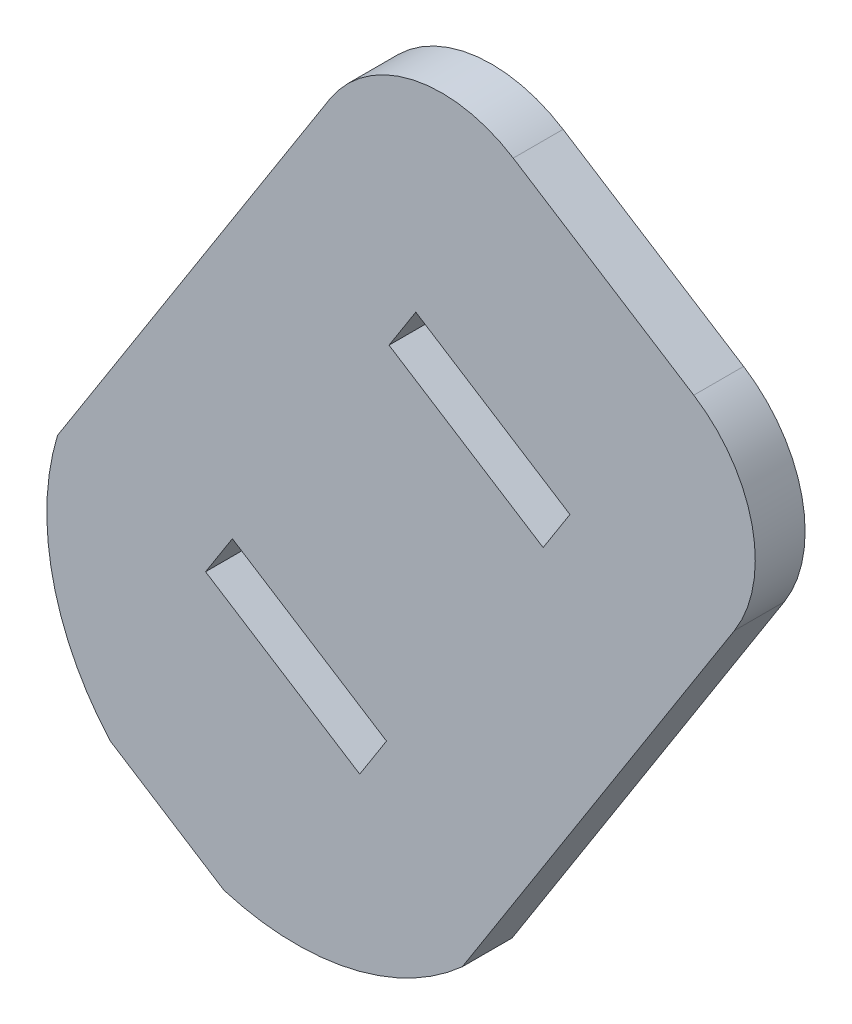
SolidWorks part; units mm, degrees
ref_plane "Alzado" through (0, 0, 0) normal (0, 0, 1) x (1, 0, 0)
ref_plane "Planta" through (0, 0, 0) normal (0, 1, 0) x (1, 0, 0)
ref_plane "Vista lateral" through (0, 0, 0) normal (1, 0, 0) x (0, 0, -1)
sketch "Croquis1" plane through (0, 0, 0) normal (0, 0, 1) x (1, 0, 0)
  circle A0 centre (-35.8759, 30.3873) radius 8
extrude "Saliente-Extruir1" add sketch "Croquis1" against normal up to surface (8 mm away)
sketch "Croquis2" plane through (0, 0, 0) normal (0, 0, 1) x (1, 0, 0)
  line L0 (-45.8794, 41.5645) -> (-50.2335, 34.73)
  line L1 (-13.9527, 57.2587) -> (-20.7873, 61.6128)
  line L2 (-25.8723, 19.2102) -> (-21.5182, 26.0447)
  line L4 (-35.8759, 30.3873) -> (-17.37, 59.4358) construction
  line L5 (-45.8794, 41.5645) -> (-33.849, 60.4485)
  line L6 (-47.0531, 20.3838) -> (-40.2185, 16.0297)
  line L7 (-25.8723, 19.2102) -> (-21.5182, 26.0447)
  line L8 (-54.8587, -26.2892) -> (-43.112, -7.8507)
  line L9 (-20.7873, 61.6128) -> (-22.8035, 62.8973)
  line L10 (-13.9527, 57.2587) -> (-11.9365, 55.9743)
  line L11 (-24.6987, 40.3909) -> (-31.5333, 44.745)
  line L12 (-21.5182, 26.0447) -> (-9.4878, 44.9287)
  arc A0 (-50.2335, 34.73) -> (-47.0531, 20.3838) centre (-35.8759, 30.3873) ccw
  arc A1 (-22.8035, 62.8973) -> (-33.849, 60.4485) centre (-27.1019, 56.1501) ccw
  arc A2 (-11.9365, 55.9743) -> (-9.4878, 44.9287) centre (-16.2349, 49.2271) cw
  arc A3 (-40.2185, 16.0297) -> (-25.8723, 19.2102) centre (-35.8759, 30.3873) ccw
  point P19 (-35.8759, 30.3873)
  dimension "D1" = 4
  dimension "D2" = 8
extrude "Saliente-Extruir2" add sketch "Croquis2" along normal blind 3
sketch "Croquis5" plane through (0, 0, 0) normal (0, 0, 1) x (1, 0, 0)
  line L0 (-19.3905, 46.0278) -> (-21.0024, 43.4976)
  line L5 (-24.0292, 48.9829) -> (-25.6411, 46.4528) construction
  line L7 (-28.6678, 51.9381) -> (-24.0292, 48.9829) construction
  line L8 (-28.6678, 51.9381) -> (-19.3905, 46.0278)
  line L9 (-28.6678, 51.9381) -> (-30.2797, 49.4079)
  line L11 (-30.2797, 49.4079) -> (-21.0024, 43.4976)
  line L12 (-30.4313, 28.6973) -> (-32.0432, 26.1671)
  line L15 (-35.0699, 31.6524) -> (-36.6818, 29.1223) construction
  line L16 (-39.7086, 34.6076) -> (-35.0699, 31.6524) construction
  line L17 (-39.7086, 34.6076) -> (-30.4313, 28.6973)
  line L18 (-39.7086, 34.6076) -> (-41.3205, 32.0774)
  line L19 (-41.3205, 32.0774) -> (-32.0432, 26.1671)
  point P1 (-24.8351, 47.7179)
  point P3 (-25.6411, 46.4528)
  point P5 (-35.8759, 30.3873)
  point P7 (-35.8759, 30.3873)
  point P9 (-36.6818, 29.1223)
extrude "Cortar-Extruir1" cut sketch "Croquis5" against normal blind 10 and the other way blind 10
